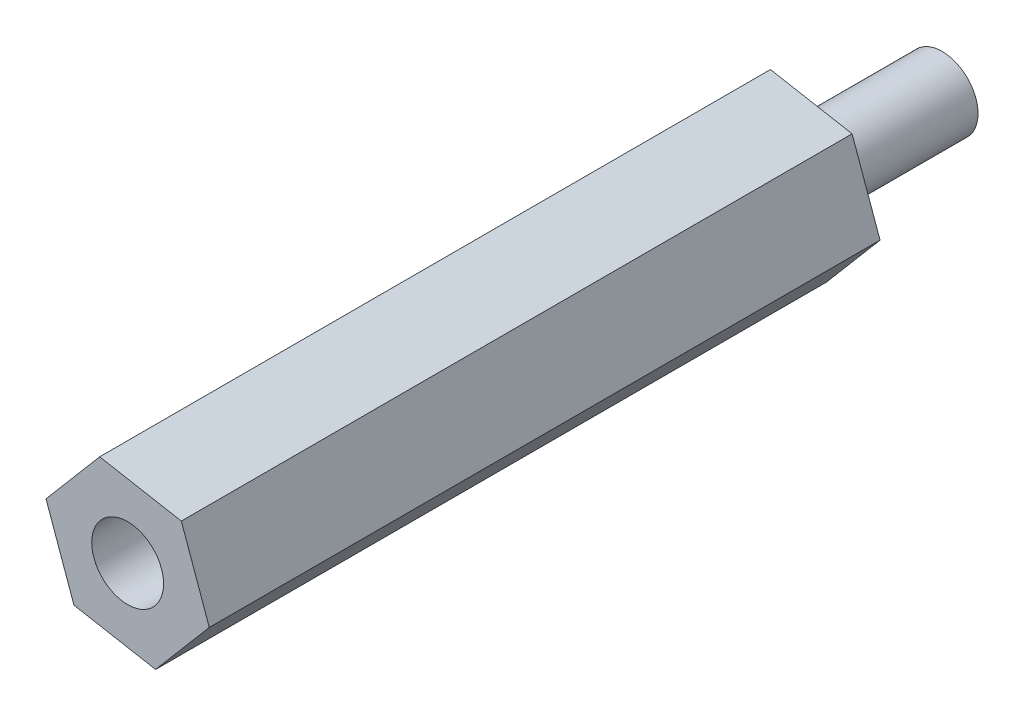
SolidWorks part; units mm, degrees
material "ABS"
ref_plane "Plano frontal" through (0, 0, 0) normal (0, 0, 1) x (1, 0, 0)
ref_plane "Plano superior" through (0, 0, 0) normal (0, 1, 0) x (1, 0, 0)
ref_plane "Plano direito" through (0, 0, 0) normal (1, 0, 0) x (0, 0, -1)
sketch "Esboço1" plane through (0, 0, 0) normal (0, 0, 1) x (1, 0, 0)
  line L1 (12.9332, -4.1439) -> (9.5251, -3.5237)
  line L2 (9.5251, -3.5237) -> (7.2839, -6.1651)
  line L3 (7.2839, -6.1651) -> (8.4508, -9.4267)
  line L4 (8.4508, -9.4267) -> (11.8589, -10.0469)
  line L5 (11.8589, -10.0469) -> (14.1001, -7.4055)
  line L6 (14.1001, -7.4055) -> (12.9332, -4.1439)
  circle A0 centre (10.692, -6.7853) radius 3 construction
extrude "Ressalto-extrusão1" add sketch "Esboço1" along normal blind 28
sketch "Esboço4" plane through (0, 0, 0) normal (0, 0, -1) x (-1, 0, 0)
  line L1 (-12.9332, -4.1439) -> (-9.5251, -3.5237) construction
  circle A0 centre (-10.692, -6.7853) radius 1.5
  dimension "D1" = 3
extrude "Corte-extrusão2" cut sketch "Esboço4" against normal blind 40
sketch "Esboço6" plane through (0, 0, 0) normal (0, 0, -1) x (-1, 0, 0)
  circle A0 centre (-10.692, -6.7853) radius 1.5
  dimension "D1" = 3
extrude "Ressalto-extrusão2" add sketch "Esboço6" along normal blind 6 separate body
